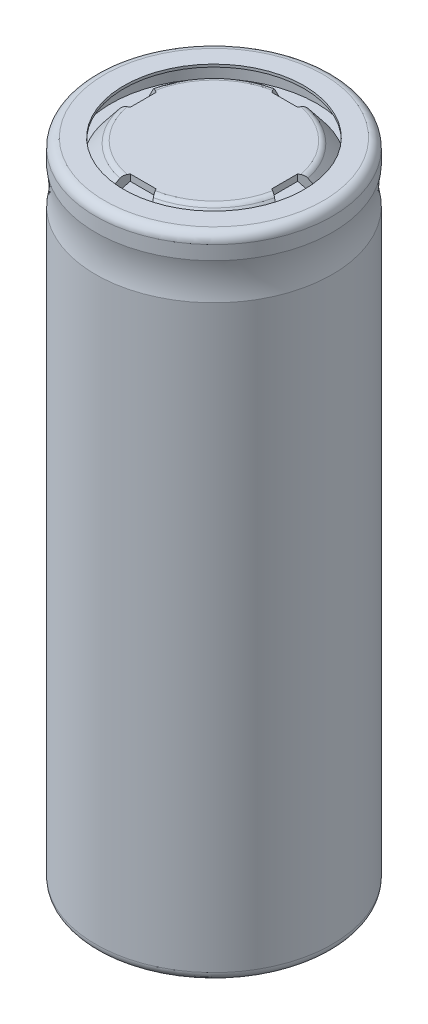
SolidWorks part; units mm, degrees
ref_plane "Спереди" through (0, 0, 0) normal (0, 0, 1) x (1, 0, 0)
ref_plane "Сверху" through (0, 0, 0) normal (0, 1, 0) x (1, 0, 0)
ref_plane "Справа" through (0, 0, 0) normal (1, 0, 0) x (0, 0, -1)
sketch "Эскиз1" plane through (0, 0, 0) normal (0, 0, 1) x (1, 0, 0)
  line L0 (0, 0) -> (0, 113.9204) construction
  line L1 (0, 0) -> (8.5, 0)
  line L2 (9, 0.5) -> (9, 45.5873)
  line L3 (8.5, 45.5873) -> (8.5, 0.5)
  line L4 (8.4985, 50.0015) -> (10.3122, 50.0015) construction
  line L5 (9, 48.4157) -> (9, 49.5)
  line L6 (0, 0) -> (0, 0.5)
  line L7 (0, 0.5) -> (8.5, 0.5)
  line L8 (7.997, 49.5) -> (7.997, 48.5)
  line L9 (8.4985, 48.4152) -> (8.4985, 49.5)
  line L10 (7.997, 48.5) -> (8.4985, 48.5)
  line L11 (8.4985, 50.0015) -> (-1.0683, 50.0015) construction
  line L12 (0, 50) -> (5.7595, 50.0014)
  line L13 (0, 50) -> (0, 49.5)
  line L14 (7.997, 48.5) -> (7.2, 48.5)
  line L15 (7.2, 48.5) -> (6.1502, 49.8136)
  line L16 (0, 49.5) -> (5.6088, 49.5)
  line L17 (7.2, 48.5) -> (7.2, 48)
  line L18 (7.2, 48) -> (8.2, 48)
  line L19 (8.2, 48) -> (8.2, 48.5)
  line L20 (5.6088, 49.5) -> (6.7, 48.5)
  line L21 (7.2, 48.5) -> (0, 48.5)
  line L22 (0, 48.5) -> (0, 48)
  line L23 (0, 48) -> (7.2, 48)
  arc A0 (9, 0.5) -> (8.5, 0) centre (8.5, 0.5) cw
  arc A1 (9, 49.5) -> (7.997, 49.5) centre (8.4985, 49.5) ccw
  arc A2 (8.6667, 47.9443) -> (8.6667, 46.0587) centre (9, 47.0015) ccw
  arc A3 (9, 48.4157) -> (8.6667, 47.9443) centre (8.5, 48.4157) cw
  arc A4 (9, 45.5873) -> (8.6667, 46.0587) centre (8.5, 45.5873) ccw
  arc A5 (8.1657, 47.9439) -> (8.1667, 46.0587) centre (8.5, 47.0015) ccw
  arc A6 (8.1667, 46.0587) -> (8.5, 45.5873) centre (8, 45.5873) cw
  arc A7 (8.4985, 48.4152) -> (8.1657, 47.9439) centre (7.9985, 48.4152) cw
  arc A8 (5.7595, 50.0014) -> (6.1502, 49.8136) centre (5.7596, 49.5014) cw
  point P7 (9, 0)
  point P18 (9, 48.0015)
  point P30 (8.4985, 48.0015)
  point P43 (6, 50.0015)
  dimension "D3" = 0.5
  dimension "D4" = 0.5015
  dimension "D5" = 1
  dimension "D7" = 0.5
  dimension "D8" = 0.5
  dimension "D14" = 1
  dimension "D12" = 0.5
  dimension "D16" = 0.5
  dimension "D24" = 0.5
  dimension "D1" = 18
  dimension "D2" = 49.5
  dimension "D6" = 2
  dimension "D9" = 2.4985
  dimension "D10" = 0.5
  dimension "D11" = 8.5
  dimension "D13" = 1
  dimension "D15" = 2.4985
  dimension "D17" = 0.5
  dimension "D18" = 12
  dimension "D19" = 0.5
  dimension "D20" = 0.5
  dimension "D21" = 1
  dimension "D22" = 0.8
  dimension "D23" = 5.6088
  dimension "D25" = 0.5
  dimension "D26" = 1
revolve "Повернуть1" add sketch "Эскиз1" angle 360 about L0
sketch "Эскиз2" plane through (0, 49.5, 0) normal (0, -1, 0) x (1, 0, 0)
  line L0 (0, -10.6971) -> (0, 9.7635) construction
  line L1 (-14.6111, 0) -> (9.951, 0) construction
  line L2 (-1, -5.4957) -> (1, -5.4957)
  line L3 (1, -5.4957) -> (2, -7.2)
  line L4 (2, -7.2) -> (-2, -7.2)
  line L5 (-1, -5.4957) -> (-2, -7.2)
  line L6 (-5.4957, 1) -> (-5.4957, -1)
  line L7 (-5.4957, -1) -> (-7.2, -2)
  line L8 (-7.2, -2) -> (-7.2, 2)
  line L9 (-5.4957, 1) -> (-7.2, 2)
  line L10 (1, 5.4957) -> (-1, 5.4957)
  line L11 (-1, 5.4957) -> (-2, 7.2)
  line L12 (-2, 7.2) -> (2, 7.2)
  line L13 (1, 5.4957) -> (2, 7.2)
  line L14 (5.4957, -1) -> (5.4957, 1)
  line L15 (5.4957, 1) -> (7.2, 2)
  line L16 (7.2, 2) -> (7.2, -2)
  line L17 (5.4957, -1) -> (7.2, -2)
  point P12 (0, -7.2)
  point P13 (0, -5.4957)
  point P20 (-7.2, 0)
  point P21 (-5.4957, 0)
  point P26 (0, 7.2)
  point P27 (0, 5.4957)
  point P32 (7.2, 0)
  point P33 (5.4957, 0)
  dimension "D1" = 1.7043
  dimension "D2" = 2
  dimension "D3" = 1
  dimension "D5" = 5.4957
  dimension "D4" = 4
extrude "Вырез-Вытянуть1" cut sketch "Эскиз2" along normal up to surface (1 mm away) and the other way through all up to face at (0, 48.5, -7.997)
sketch "Эскиз3" plane through (0, 0, 0) normal (0, 0, 1) x (1, 0, 0)
  line L0 (0, -2.74) -> (0, 74.3076) construction
  line L1 (9, 49.5) -> (9, 48.4157)
  line L2 (8.4977, 0) -> (7, 0)
  line L3 (9, 49.5) -> (9, 48.4157)
  line L4 (9, 45.5873) -> (9, 0.5)
  line L5 (9, 45.5873) -> (9, 0.5)
  line L6 (8.5953, 0.0092) -> (8.4977, 0)
  line L7 (8.5953, 0.0092) -> (8.4977, 0)
  line L8 (8.4977, 0) -> (-8.5, 0)
  line L10 (-9, 0.5) -> (-9, 45.5873)
  line L12 (-9, 48.4157) -> (-9, 49.5)
  line L14 (-8.5941, 49.9923) -> (8.4962, 50.0015)
  line L16 (-8.5, 0) -> (8.5, 0) construction
  line L17 (7, 0) -> (7, -0.2)
  line L18 (7, -0.2) -> (8.5, -0.2)
  line L19 (9.2, 0.5) -> (9.2, 45.5873)
  line L20 (8.4985, 49.5) -> (8.4985, 65.4748) construction
  line L21 (9.2, 48.4163) -> (9.2, 49.5)
  line L22 (9, 0.5) -> (9.2, 0.5) construction
  line L23 (7, 50.0015) -> (8.4962, 50.0015)
  line L24 (8.4985, 50.0015) -> (-8.4985, 50.0015) construction
  line L25 (7, 50.0015) -> (7, 50.2015)
  line L26 (7, 50.2015) -> (8.4985, 50.2015)
  arc A0 (8.6667, 47.9443) -> (9, 48.4157) centre (8.5, 48.4157) ccw
  arc A2 (8.6667, 47.9443) -> (8.6667, 46.0587) centre (9, 47.0015) ccw
  arc A4 (9, 45.5873) -> (8.6667, 46.0587) centre (8.5, 45.5873) ccw
  arc A6 (8.5953, 0.0092) -> (9, 0.5) centre (8.5, 0.5) ccw
  arc A7 (8.5953, 0.0092) -> (9, 0.5) centre (8.5, 0.5) ccw
  arc A8 (-9, 0.5) -> (-8.5, 0) centre (-8.5, 0.5) ccw
  arc A10 (-8.6667, 46.0587) -> (-9, 45.5873) centre (-8.5, 45.5873) ccw
  arc A12 (-8.6667, 46.0587) -> (-8.6667, 47.9443) centre (-9, 47.0015) ccw
  arc A14 (-9, 48.4157) -> (-8.6667, 47.9443) centre (-8.5, 48.4157) ccw
  arc A16 (-8.5941, 49.9923) -> (-9, 49.5) centre (-8.4985, 49.5) ccw
  arc A18 (9, 49.5) -> (8.4962, 50.0015) centre (8.4985, 49.5) ccw
  arc A19 (9, 49.5) -> (8.4962, 50.0015) centre (8.4985, 49.5) ccw
  arc A21 (8.4985, 50.2015) -> (9.2, 49.5) centre (8.4985, 49.5) cw
  arc A22 (8.5, -0.2) -> (9.2, 0.5) centre (8.5, 0.5) ccw
  spline S0 degree 2 poles (9, 48.4157) (8.6971, 46.9443) (9, 45.5873) knots 0 0 0 0.587528 0.587528 0.587528
  spline S1 degree 2 poles (9.2, 48.4163) (8.9014, 46.9539) (9.2, 45.5873) knots 0 0 0 0.679955 0.679955 0.679955
  dimension "D1" = 7
  dimension "D2" = 0.2
  dimension "D5" = 0.2
  dimension "D7" = 49
  dimension "D4" = 49
  dimension "D6" = 7
  dimension "D8" = 0.2
revolve "Повернуть4" add sketch "Эскиз3" angle 360 about L0
equation "\"D8@Эскиз1\"=\"D7@Эскиз1\""
equation "\"D14@Эскиз1\"=\"D5@Эскиз1\""
equation "\"D15@Эскиз1\"=\"D9@Эскиз1\""
equation "\"D12@Эскиз1\"=\"D7@Эскиз1\""
equation "\"D16@Эскиз1\"=\"D7@Эскиз1\""
equation "\"D17@Эскиз1\"=\"D10@Эскиз1\""
equation "\"D7@Эскиз3\"=\"D4@Эскиз3\""
equation "\"D8@Эскиз3\"=\"D5@Эскиз3\""
